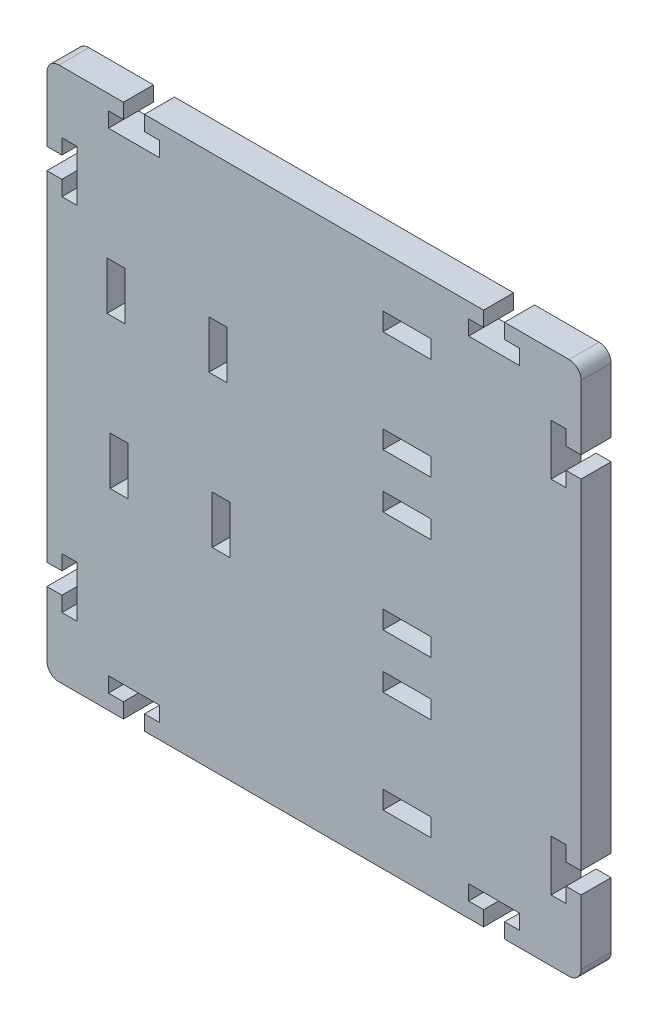
SolidWorks part; units mm, degrees
ref_plane "Спереди" through (0, 0, 0) normal (0, 0, 1) x (1, 0, 0)
ref_plane "Сверху" through (0, 0, 0) normal (0, 1, 0) x (1, 0, 0)
ref_plane "Справа" through (0, 0, 0) normal (1, 0, 0) x (0, 0, -1)
sketch "Эскиз1" plane through (0, 0, 0) normal (0, 0, 1) x (1, 0, 0)
  line L0 (-31.75, 40.3401) -> (-42.5, 40.3401)
  line L1 (-28.25, 37.8401) -> (-25.75, 37.8401)
  line L2 (0, 0) -> (0, 20.4288) construction
  line L3 (0, 0) -> (17.3357, 0) construction
  line L4 (25.75, 37.8401) -> (25.75, 35.3401)
  line L5 (34.25, 35.3401) -> (25.75, 35.3401)
  line L6 (34.25, 37.8401) -> (34.25, 35.3401)
  line L7 (-31.75, 40.3401) -> (-31.75, 37.8401)
  line L8 (34.25, 37.8401) -> (31.75, 37.8401)
  line L9 (28.25, 40.3401) -> (28.25, 37.8401)
  line L10 (31.75, 40.3401) -> (31.75, 37.8401)
  line L11 (-28.25, 40.3401) -> (-28.25, 37.8401)
  line L12 (-34.25, 37.8401) -> (-31.75, 37.8401)
  line L13 (-34.25, 37.8401) -> (-34.25, 35.3401)
  line L14 (-34.25, 35.3401) -> (-25.75, 35.3401)
  line L15 (-25.75, 37.8401) -> (-25.75, 35.3401)
  line L16 (28.25, 37.8401) -> (25.75, 37.8401)
  line L17 (42, 24.0901) -> (42, 21.5901)
  line L18 (42, -29.9099) -> (39.5, -29.9099)
  line L19 (39.5, -38.4099) -> (39.5, -29.9099)
  line L20 (42, -38.4099) -> (39.5, -38.4099)
  line L21 (44.5, 27.5901) -> (42, 27.5901)
  line L22 (42.5, -48.6599) -> (31.75, -48.6599)
  line L23 (44.5, -46.6599) -> (44.5, -35.9099)
  line L24 (42.5, 40.3401) -> (31.75, 40.3401)
  line L25 (-44.5, -32.4099) -> (-44.5, 24.0901)
  line L26 (42, -38.4099) -> (42, -35.9099)
  line L27 (44.5, -32.4099) -> (42, -32.4099)
  line L28 (44.5, -35.9099) -> (42, -35.9099)
  line L29 (44.5, 24.0901) -> (42, 24.0901)
  line L30 (42, 30.0901) -> (42, 27.5901)
  line L31 (42, 30.0901) -> (39.5, 30.0901)
  line L32 (39.5, 30.0901) -> (39.5, 21.5901)
  line L33 (42, 21.5901) -> (39.5, 21.5901)
  line L34 (42, -32.4099) -> (42, -29.9099)
  line L35 (28.25, -46.1599) -> (25.75, -46.1599)
  line L36 (-25.75, -46.1599) -> (-25.75, -43.6599)
  line L37 (-34.25, -43.6599) -> (-25.75, -43.6599)
  line L38 (-34.25, -46.1599) -> (-34.25, -43.6599)
  line L39 (31.75, -48.6599) -> (31.75, -46.1599)
  line L40 (-34.25, -46.1599) -> (-31.75, -46.1599)
  line L41 (-28.25, -48.6599) -> (-28.25, -46.1599)
  line L42 (-31.75, -48.6599) -> (-31.75, -46.1599)
  line L43 (28.25, -48.6599) -> (28.25, -46.1599)
  line L44 (34.25, -46.1599) -> (31.75, -46.1599)
  line L45 (34.25, -46.1599) -> (34.25, -43.6599)
  line L46 (34.25, -43.6599) -> (25.75, -43.6599)
  line L47 (25.75, -46.1599) -> (25.75, -43.6599)
  line L48 (-28.25, -46.1599) -> (-25.75, -46.1599)
  line L49 (-44.5, 27.5901) -> (-44.5, 38.3401)
  line L50 (-42, -32.4099) -> (-42, -29.9099)
  line L51 (-42, 21.5901) -> (-39.5, 21.5901)
  line L52 (-39.5, 30.0901) -> (-39.5, 21.5901)
  line L53 (-34.5, 16.5) -> (-13.9619, -16.5) construction
  line L54 (-42, 30.0901) -> (-42, 27.5901)
  line L55 (-44.5, 24.0901) -> (-42, 24.0901)
  line L56 (-44.5, -35.9099) -> (-42, -35.9099)
  line L57 (-44.5, -32.4099) -> (-42, -32.4099)
  line L58 (-42, 30.0901) -> (-39.5, 30.0901)
  line L59 (-42, -38.4099) -> (-42, -35.9099)
  line L60 (-44.5, -46.6599) -> (-44.5, -35.9099)
  line L61 (-44.5, 27.5901) -> (-42, 27.5901)
  line L62 (-42, -38.4099) -> (-39.5, -38.4099)
  line L63 (28.25, 40.3401) -> (-28.25, 40.3401)
  line L64 (44.5, 27.5901) -> (44.5, 38.3401)
  line L65 (44.5, -32.4099) -> (44.5, 24.0901)
  line L66 (28.25, -48.6599) -> (-28.25, -48.6599)
  line L67 (-31.75, -48.6599) -> (-42.5, -48.6599)
  line L68 (-42, -32.4099) -> (-42, -29.9099) [skipped]
  line L69 (-44.5, -35.9099) -> (-42, -35.9099) [skipped]
  line L70 (-44.5, -32.4099) -> (-42, -32.4099) [skipped]
  line L71 (-42, -38.4099) -> (-42, -35.9099) [skipped]
  line L72 (-42, -38.4099) -> (-39.5, -38.4099) [skipped]
  line L73 (-39.5, -38.4099) -> (-39.5, -29.9099) [skipped]
  line L74 (-42, -29.9099) -> (-39.5, -29.9099) [skipped]
  line L75 (-42, 21.5901) -> (-39.5, 21.5901) [skipped]
  line L76 (-39.5, 30.0901) -> (-39.5, 21.5901) [skipped]
  line L77 (-42, 30.0901) -> (-39.5, 30.0901) [skipped]
  line L78 (-42, 30.0901) -> (-42, 27.5901) [skipped]
  line L79 (-44.5, 24.0901) -> (-42, 24.0901) [skipped]
  line L80 (-44.5, 27.5901) -> (-42, 27.5901) [skipped]
  line L81 (-42, 24.0901) -> (-42, 21.5901) [skipped]
  line L82 (-39.5, -38.4099) -> (-39.5, -29.9099)
  line L83 (-42, -29.9099) -> (-39.5, -29.9099)
  line L84 (-42, 24.0901) -> (-42, 21.5901)
  line L85 (15.5, 12.2701) -> (15.5, 31.41) construction
  line L86 (-34.5, 16.5) -> (-31.5, 16.5)
  line L87 (-34.5, 16.5) -> (-34.5, 8.5)
  line L88 (-34.5, 8.5) -> (-31.5, 8.5)
  line L89 (-31.5, 16.5) -> (-31.5, 8.5)
  line L90 (-34.5, 16.5) -> (-31.5, 8.5) construction
  line L91 (-34.5, 8.5) -> (-31.5, 16.5) construction
  line L92 (-33.9619, -8.5) -> (-30.9619, -8.5)
  line L93 (-33.9619, -8.5) -> (-33.9619, -16.5)
  line L94 (-33.9619, -16.5) -> (-30.9619, -16.5)
  line L95 (-30.9619, -8.5) -> (-30.9619, -16.5)
  line L96 (-33.9619, -8.5) -> (-30.9619, -16.5) construction
  line L97 (-33.9619, -16.5) -> (-30.9619, -8.5) construction
  line L98 (-17.5, 16.5) -> (-14.5, 16.5)
  line L99 (-17.5, 16.5) -> (-17.5, 8.5)
  line L100 (-17.5, 8.5) -> (-14.5, 8.5)
  line L101 (-14.5, 16.5) -> (-14.5, 8.5)
  line L102 (-17.5, 16.5) -> (-14.5, 8.5) construction
  line L103 (-17.5, 8.5) -> (-14.5, 16.5) construction
  line L104 (-16.9619, -8.5) -> (-13.9619, -8.5)
  line L105 (-16.9619, -8.5) -> (-16.9619, -16.5)
  line L106 (-16.9619, -16.5) -> (-13.9619, -16.5)
  line L107 (-13.9619, -8.5) -> (-13.9619, -16.5)
  line L108 (-16.9619, -8.5) -> (-13.9619, -16.5) construction
  line L109 (-16.9619, -16.5) -> (-13.9619, -8.5) construction
  line L116 (15.5, 21.8401) -> (29.9629, 21.8401) construction
  line L117 (19.5, 14.8401) -> (19.5, 11.8401)
  line L118 (11.5, 28.8401) -> (19.5, 28.8401)
  line L119 (11.5, 28.8401) -> (11.5, 31.8401)
  line L120 (11.5, 31.8401) -> (19.5, 31.8401)
  line L121 (19.5, 28.8401) -> (19.5, 31.8401)
  line L122 (11.5, 28.8401) -> (19.5, 31.8401) construction
  line L123 (11.5, 31.8401) -> (19.5, 28.8401) construction
  line L124 (11.5, 11.8401) -> (19.5, 14.8401) construction
  line L125 (11.5, 14.8401) -> (19.5, 11.8401) construction
  line L126 (11.5, 11.8401) -> (19.5, 11.8401)
  line L127 (11.5, 14.8401) -> (11.5, 11.8401)
  line L128 (11.5, 14.8401) -> (19.5, 14.8401)
  line L129 (-14.5, 16.5) -> (-33.9619, -16.5) construction
  line L133 (19.5, -11.1599) -> (19.5, -14.1599)
  line L134 (11.5, 2.8401) -> (19.5, 2.8401)
  line L135 (11.5, 2.8401) -> (11.5, 5.8401)
  line L136 (11.5, 5.8401) -> (19.5, 5.8401)
  line L137 (19.5, 2.8401) -> (19.5, 5.8401)
  line L138 (11.5, -14.1599) -> (19.5, -14.1599)
  line L139 (11.5, -11.1599) -> (11.5, -14.1599)
  line L140 (11.5, -11.1599) -> (19.5, -11.1599)
  line L141 (15.5, -13.7299) -> (15.5, 5.41) construction
  line L144 (15.5, -4.1599) -> (29.9629, -4.1599) construction
  line L145 (11.5, 2.8401) -> (19.5, 5.8401) construction
  line L146 (11.5, 5.8401) -> (19.5, 2.8401) construction
  line L147 (11.5, -14.1599) -> (19.5, -11.1599) construction
  line L148 (11.5, -11.1599) -> (19.5, -14.1599) construction
  line L153 (19.5, -37.1599) -> (19.5, -40.1599)
  line L154 (11.5, -23.1599) -> (19.5, -23.1599)
  line L155 (11.5, -23.1599) -> (11.5, -20.1599)
  line L156 (11.5, -20.1599) -> (19.5, -20.1599)
  line L157 (19.5, -23.1599) -> (19.5, -20.1599)
  line L158 (11.5, -40.1599) -> (19.5, -40.1599)
  line L159 (11.5, -37.1599) -> (11.5, -40.1599)
  line L160 (11.5, -37.1599) -> (19.5, -37.1599)
  line L161 (15.5, -39.7299) -> (15.5, -20.59) construction
  line L164 (15.5, -30.1599) -> (29.9629, -30.1599) construction
  line L165 (11.5, -23.1599) -> (19.5, -20.1599) construction
  line L166 (11.5, -20.1599) -> (19.5, -23.1599) construction
  line L167 (11.5, -40.1599) -> (19.5, -37.1599) construction
  line L168 (11.5, -37.1599) -> (19.5, -40.1599) construction
  arc A0 (-44.5, -46.6599) -> (-42.5, -48.6599) centre (-42.5, -46.6599) ccw
  arc A1 (42.5, -48.6599) -> (44.5, -46.6599) centre (42.5, -46.6599) ccw
  arc A2 (44.5, 38.3401) -> (42.5, 40.3401) centre (42.5, 38.3401) ccw
  arc A3 (-42.5, 40.3401) -> (-44.5, 38.3401) centre (-42.5, 38.3401) ccw
  point P72 (-33, 12.5)
  point P75 (0, -4.1599)
  point P106 (-32.4619, -12.5)
  point P111 (-16, 12.5)
  point P116 (-15.4619, -12.5)
  point P123 (-44.5, -48.6599)
  point P126 (44.5, -48.6599)
  point P129 (44.5, 40.3401)
  point P132 (-44.5, 40.3401)
  point P133 (15.5, 21.8401)
  point P141 (15.5, 30.3401)
  point P151 (15.5, 13.3401)
  point P154 (15.5, -4.1599)
  point P162 (15.5, 4.3401)
  point P172 (15.5, -12.6599)
  point P173 (15.5, -30.1599)
  point P181 (15.5, -21.6599)
  point P191 (15.5, -38.6599)
  dimension "D3" = 3.5
  dimension "D6" = 2.5
  dimension "D9" = 17
  dimension "D14" = 8
  dimension "D26" = 2
  dimension "D2" = 12.75
  dimension "D4" = 2.5
  dimension "D5" = 17
  dimension "D7" = 8.5
  dimension "D8" = 89
  dimension "D10" = 8
  dimension "D11" = 4
  dimension "D12" = 89
  dimension "D13" = 3
  dimension "D15" = 3
  dimension "D16" = 25
  dimension "D17" = 3
  dimension "D18" = 8
  dimension "D19" = 8
  dimension "D20" = 3
  dimension "D21" = 25
  dimension "D22" = 0
  dimension "D23" = 10
  dimension "D24" = 8.5
  dimension "D25" = 2.5
  dimension "D27" = 25
  dimension "D29" = 8
  dimension "D30" = 3
  dimension "D31" = 8.5
  dimension "D32" = 3
extrude "Бобышка-Вытянуть1" add sketch "Эскиз1" along normal blind 5
